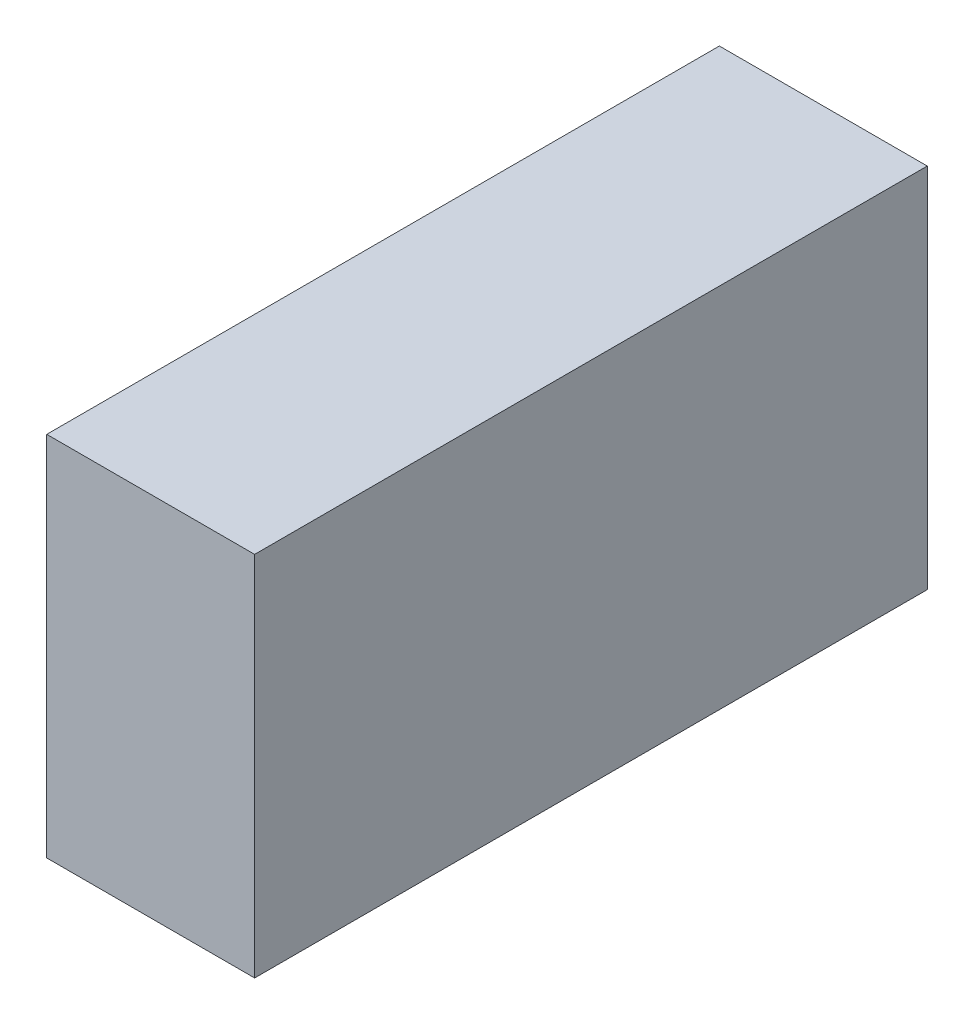
SolidWorks part; units mm, degrees
ref_plane "Plan de face" through (0, 0, 0) normal (0, 0, 1) x (1, 0, 0)
ref_plane "Plan de dessus" through (0, 0, 0) normal (0, 1, 0) x (1, 0, 0)
ref_plane "Plan de droite" through (0, 0, 0) normal (1, 0, 0) x (0, 0, -1)
sketch "Esquisse1" plane through (0, -86.358, 0) normal (0, 1, 0) x (1, 0, 0)
  line L1 (-52.2058, -7.8456) -> (-35.2058, -7.8456)
  line L2 (-52.2058, -7.8456) -> (-52.2058, -62.8456)
  line L3 (-52.2058, -62.8456) -> (-35.2058, -62.8456)
  line L4 (-35.2058, -7.8456) -> (-35.2058, -62.8456)
  dimension "D1" = 17
  dimension "D2" = 55
extrude "Boss.-Extru.1" add sketch "Esquisse1" along normal blind 30
